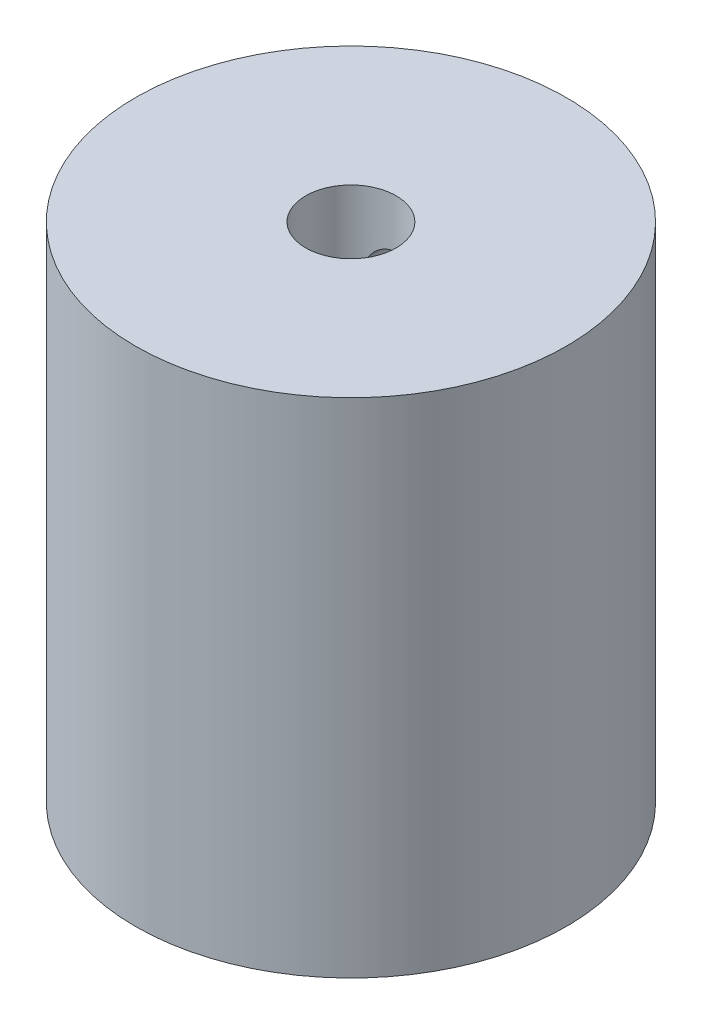
SolidWorks part; units mm, degrees
material "6061 Alloy"
ref_plane "Front Plane" through (0, 0, 0) normal (0, 0, 1) x (1, 0, 0)
ref_plane "Top Plane" through (0, 0, 0) normal (0, 1, 0) x (1, 0, 0)
ref_plane "Right Plane" through (0, 0, 0) normal (1, 0, 0) x (0, 0, -1)
sketch "Sketch1" plane through (0, 0, 0) normal (0, 1, 0) x (1, 0, 0)
  circle A0 centre (0, 0) radius 19.05
  dimension "D1" = 38.1
extrude "Boss-Extrude1" add sketch "Sketch1" along normal blind 50.8
sketch "Sketch2" plane through (0, 50.8, 0) normal (0, 1, 0) x (1, 0, 0)
  circle A0 centre (0, 0) radius 4
  dimension "D1" = 8
extrude "Cut-Extrude1" cut sketch "Sketch2" against normal blind 25.4
sketch "Sketch3" plane through (0, 0, 0) normal (0, -1, 0) x (-1, 0, 0)
  line L0 (0, 0) -> (0, 19.05) construction
  circle A0 centre (0, 0) radius 19.05 construction
  point P0 (0, 0)
ref_plane "Plane1" through (0, 0, -19.05) normal (0, 0, -1) x (-1, 0, 0)
sketch "Sketch4" plane through (0, 0, -19.05) normal (0, 0, -1) x (-1, 0, 0)
  line L0 (0, 0) -> (0, 50.8) construction
  line L1 (-19.05, 0) -> (19.05, 0) construction
  circle A0 centre (0, 12.7) radius 4
  circle A1 centre (0.1885, 38.1) radius 2
  point P7 (0, 38.1)
  dimension "D3" = 8
  dimension "D5" = 4
  dimension "D1" = 50.8
  dimension "D2" = 12.7
  dimension "D4" = 12.7
extrude "Cut-Extrude2" cut sketch "Sketch4" against normal blind 25.4
sketch "Sketch6" plane through (0, 0, 0) normal (0, -1, 0) x (1, 0, 0)
  circle A0 centre (0, 0) radius 2
  point P0 (0, 0)
  dimension "D1" = 4
extrude "Cut-Extrude3" cut sketch "Sketch6" against normal blind 12.7
sketch "Sketch7" plane through (0, 50.8, 0) normal (0, 1, 0) x (1, 0, 0)
  circle A0 centre (0, 0) radius 19.05
extrude "Cut-Extrude4" cut sketch "Sketch7" against normal blind 6.35
